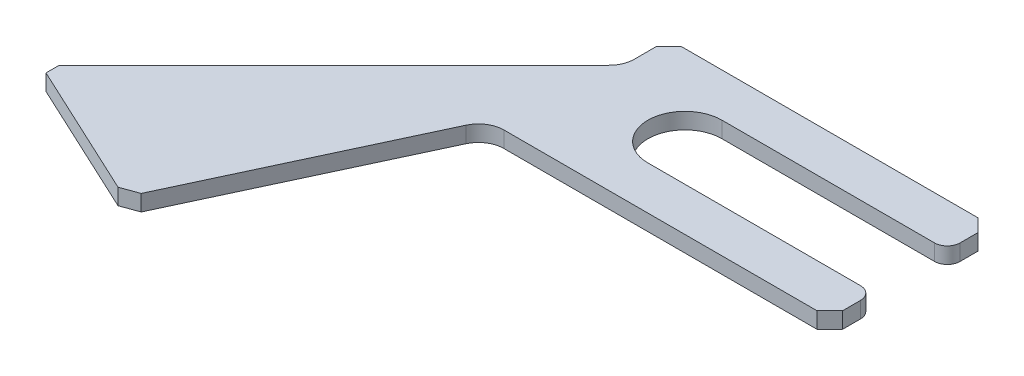
SolidWorks part; units mm, degrees
material "6061-T6 Al"
ref_plane "Front" through (0, 0, 0) normal (0, 0, 1) x (1, 0, 0)
ref_plane "Top" through (0, 0, 0) normal (0, 1, 0) x (1, 0, 0)
ref_plane "Right" through (0, 0, 0) normal (1, 0, 0) x (0, 0, -1)
sketch "Sketch1" plane through (0, 0, 0) normal (0, 1, 0) x (1, 0, 0)
  line L0 (-11.68, -5.9166) -> (-18.4337, -20.4)
  line L1 (-10.2413, -5) -> (10, -5)
  line L2 (-10, 2.865) -> (-10, 5)
  line L3 (-10, 5) -> (10, 5)
  line L4 (10, -5) -> (10, 5)
  line L5 (-18.4337, -20.4) -> (-28.1, -15.8926)
  line L6 (-28.1, -15.8926) -> (-10.465, 1.7425)
  arc A0 (-11.68, -5.9166) -> (-10.2413, -5) centre (-10.2413, -6.5875) cw
  arc A1 (-10, 2.865) -> (-10.465, 1.7425) centre (-11.5875, 2.865) cw
  point P0 (0, 0)
  dimension "D6" = 1.5875
  dimension "D2" = 10
  dimension "D3" = 10
  dimension "D4" = 5
  dimension "D5" = 20
  dimension "D7" = 20.2413
  dimension "D8" = 38.1
  dimension "D9" = 115
  dimension "D10" = 25.4
  dimension "D11" = 20
extrude "Boss-Extrude1" add sketch "Sketch1" along normal blind 1
sketch "Sketch2" plane through (0, 1, 0) normal (0, 1, 0) x (1, 0, 0)
  line L0 (-4, 0) -> (9.207, 0) construction
  line L1 (-4, 2.3) -> (10, 2.3)
  line L2 (-4, -2.3) -> (10, -2.3)
  line L3 (10, 2.3) -> (10, -2.3)
  line L4 (10, -5) -> (10, 5) construction
  arc A0 (-4, 2.3) -> (-4, -2.3) centre (-4, 0) ccw
  point P2 (1.9116, 1.1787)
  dimension "D1" = 4.6
  dimension "D2" = 2.3
  dimension "D3" = 14
extrude "Cut-Extrude1" cut sketch "Sketch2" against normal through all
fillet "Fillet1" radius 0.7937 2 edges at (10, 0.5, 2.3) (10, 0.5, -2.3)
chamfer "Chamfer1" distance 0.7937 angle 45 5 edges at (-28.1, 0.5, 15.8926) (-18.4337, 0.5, 20.4) (-10, 0.5, -5) (10, 0.5, -5) (10, 0.5, 5)
